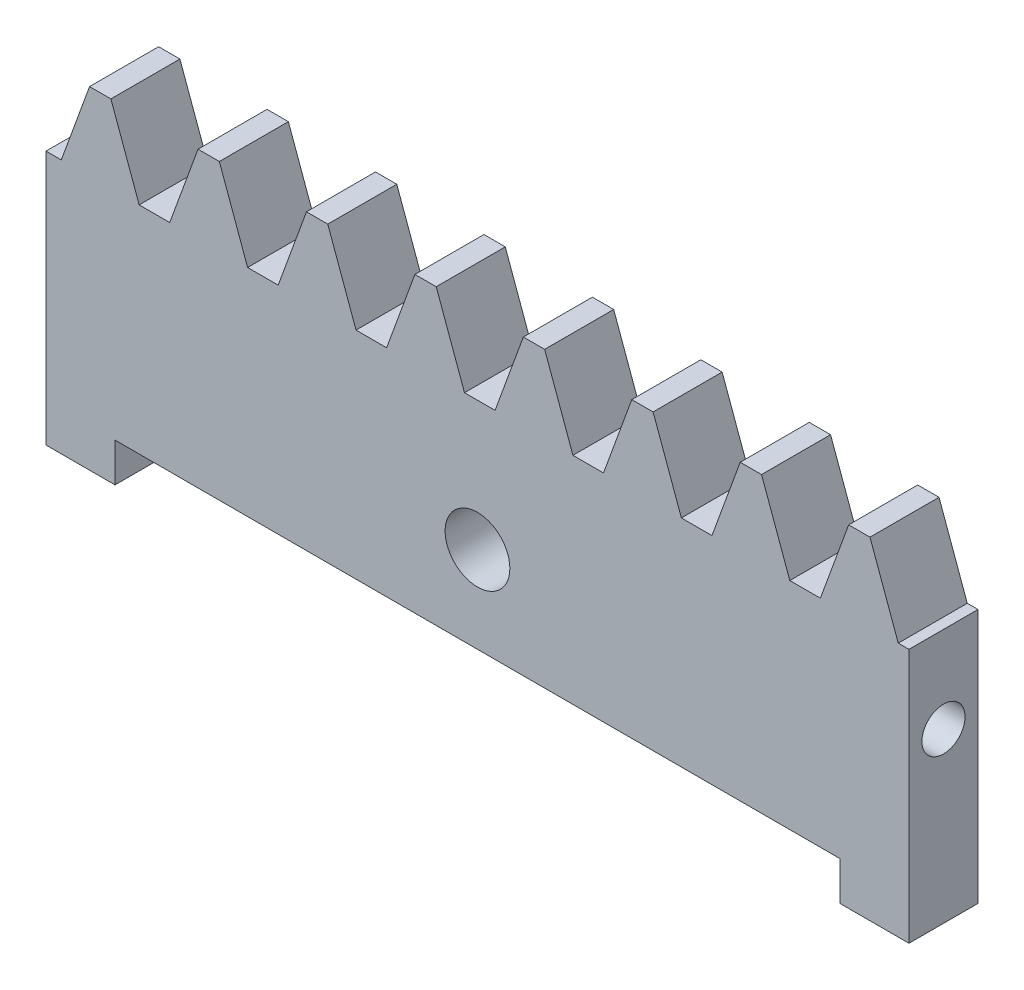
SolidWorks part; units mm, degrees
extrude "Blank" add sketch "BlankSke" against normal blind 10.16
sketch "BlankSke" plane through (0, 0, 0) normal (0, 0, 1) x (1, 0, 0)
  line L1 (0, 0) -> (127, 0)
  line L2 (0, 0) -> (0, 43.18)
  line L3 (0, 43.18) -> (127, 43.18)
  line L4 (127, 0) -> (127, 43.18)
  dimension "Length" = 127
  dimension "Blank_height" = 43.18
ref_plane "Plane1" through (0, 0, 0) normal (0, 0, 1) x (1, 0, 0)
ref_plane "Plane2" through (0, 0, 0) normal (0, 1, 0) x (1, 0, 0)
ref_plane "Plane3" through (0, 0, 0) normal (1, 0, 0) x (0, 0, -1)
other "Configuration Table"
sketch "HoldingSke" plane through (0, 0, 0) normal (0, 1, 0) x (1, 0, 0)
  line L0 (0, 0) -> (97.2876, -81.634)
  line L1 (-15, 0) -> (100, 0) construction
  line L2 (0, 0) -> (-2.1039, 2.3779)
  line L3 (0, 0) -> (-11.863, 4.5341)
  line L4 (0, 0) -> (8.5297, 1.351)
  line L5 (0, 0) -> (-23.7986, -8.8762)
  line L6 (0, 0) -> (-10.5278, -7.1032)
  line L9 (-71.009, 38.7566) -> (48.332, 82.1932)
  line L10 (-76.2, 71.12) -> (-38.1, 71.12)
  line L11 (0, 0) -> (-10.16, 0)
  line L12 (-76.2, 101.6) -> (-76.0095, 101.6)
  line L13 (24.9733, 27.94) -> (52.9518, 28.4284)
  line L14 (24.9733, 27.94) -> (24.9746, 27.94)
  line L15 (24.9733, 27.94) -> (100.4006, 29.5858)
  circle A0 centre (0, 0) radius 19.05
  circle A1 centre (0, 0) radius 19.05
  circle A2 centre (0, 0) radius 12.7
  dimension "MPH" = 38.1
  dimension "Diameter" = 38.1
  dimension "Num_teeth" = 9
  dimension "Pitch" = 127
  dimension "Show_teeth" = 400
  dimension "Thickness" = 12.7
  dimension "Ap" = 20
  dimension "Pitch_height" = 38.1
  dimension "Width" = 10.16
  dimension "Backlash" = 0.1905
  dimension "Addendum_fac" = 1
  dimension "Dedendum_fac" = 1.25
  dimension "Clearance_fac" = 0.25
  dimension "Dedendum_add" = 0.0013
  dimension "Length" = 127
sketch "TooCutSkeIll" plane through (0, 0, 0) normal (0, 0, 1) x (1, 0, 0)
  line L0 (-6.3616, 43.0463) -> (-2.5546, 32.5865)
  line L1 (-1.36, 31.75) -> (1.36, 31.75)
  line L2 (2.5546, 32.5865) -> (6.3616, 43.0463)
  line L3 (127, 43.18) -> (0, 43.18) construction
  line L4 (0, 0) -> (0, 64.897) construction
  line L5 (-13.208, 38.1) -> (12.954, 38.1) construction
  line L6 (0, 0) -> (127, 0) construction
  line L7 (4.5613, 38.1) -> (4.5613, 48.7463) construction
  line L8 (-4.5613, 38.1) -> (-4.5613, 48.7463) construction
  line L9 (6.5526, 43.18) -> (6.5526, 43.2054)
  line L10 (-6.5526, 43.18) -> (-6.5526, 43.2054)
  line L11 (-6.5526, 43.2054) -> (6.5526, 43.2054)
  arc A0 (1.36, 31.75) -> (2.5546, 32.5865) centre (1.36, 33.0213) ccw
  arc A1 (-2.5546, 32.5865) -> (-1.36, 31.75) centre (-1.36, 33.0213) ccw
  arc A2 (6.5526, 43.18) -> (6.3616, 43.0463) centre (6.5526, 42.9768) ccw
  arc A3 (-6.3616, 43.0463) -> (-6.5526, 43.18) centre (-6.5526, 42.9768) ccw
  dimension "Pitch_height" = 38.1
  dimension "Addendum_plus" = 5.1054
  dimension "Pressure_angle" = 20
  dimension "Gap_width" = 9.1226
  dimension "Dedendum" = 6.35
extrude "ToothCutIll" [suppressed] cut sketch "TooCutSkeIll" against normal through all
sketch "TooCutSkeSim" plane through (0, 0, 0) normal (0, 0, 1) x (1, 0, 0)
  line L0 (2.2501, 31.75) -> (-2.2501, 31.75)
  line L1 (6.4195, 43.2054) -> (2.2501, 31.75)
  line L2 (0, 17.4625) -> (0, 53.467) construction
  line L3 (6.4195, 43.2054) -> (-6.4195, 43.2054)
  line L6 (-6.4195, 43.2054) -> (-2.2501, 31.75)
  line L9 (-4.5613, 38.1) -> (4.5613, 38.1) construction
  line L10 (0, 0) -> (127, 0) construction
  line L11 (4.5613, 38.1) -> (4.5613, 53.467) construction
  line L12 (-4.5613, 38.1) -> (-4.5613, 53.467) construction
  dimension "Pitch_height" = 38.1
  dimension "Addendum_plus" = 5.1054
  dimension "Pressure_angle" = 20
  dimension "Gap_width" = 9.1226
  dimension "Dedendum" = 6.35
extrude "ToothCutSim" cut sketch "TooCutSkeSim" against normal through all
pattern_linear "TeethCuts" count 9 spacing 15.9593 along (1, 0, 0) of "ToothCutIll", "ToothCutSim"
sketch "Sketch1" plane through (0, 0, 0) normal (0, -1, 0) x (1, 0, 0)
  line L0 (0, -10.16) -> (127, -10.16) construction
  line L1 (0, 0) -> (10.16, 0)
  line L2 (0, 0) -> (0, -10.16)
  line L3 (0, -10.16) -> (10.16, -10.16)
  line L4 (10.16, 0) -> (10.16, -10.16)
  line L6 (127, 0) -> (116.84, 0)
  line L7 (127, 0) -> (127, -10.16)
  line L8 (127, -10.16) -> (116.84, -10.16)
  line L9 (116.84, 0) -> (116.84, -10.16)
  dimension "D1" = 10.16
sketch "Sketch4" plane through (0, 0, 0) normal (-1, 0, 0) x (0, 0, 1)
  line L0 (-10.16, 0) -> (0, 0) construction
  line L1 (-10.16, 31.75) -> (-10.16, 0) construction
  circle A0 centre (-5.08, 19.05) radius 3.175
  dimension "D2" = 6.35
  dimension "D1" = 19.05
  dimension "D3" = 5.08
extrude "Cut-Extrude2" cut sketch "Sketch4" against normal through all
extrude "Boss-Extrude1" add sketch "Sketch1" along normal blind 5.715
sketch "Sketch5" plane through (0, 0, 0) normal (0, 0, 1) x (1, 0, 0)
  line L0 (10.16, 0) -> (116.84, 0) construction
  circle A0 centre (63.5, 12.7) radius 4.7625
  dimension "D1" = 9.525
  dimension "D2" = 12.7
extrude "Cut-Extrude3" cut sketch "Sketch5" against normal through all
equation "' \"Pitch@HoldingSke\" = 4"
equation "' \"Num_teeth@HoldingSke\" = 12"
equation "' \"Ap@HoldingSke\" =  20"
equation "' \"Ap@HoldingSke\" = 20"
equation "' \"Width@HoldingSke\" = 0.25"
equation "' \"Show_teeth@HoldingSke\" = 500"
equation "' \"Backlash@HoldingSke\" = 0.009"
equation "' \"Addendum_fac@HoldingSke\" = 1.0"
equation "' \"Dedendum_fac@HoldingSke\" = 1.25"
equation "' \"Dedendum_add@HoldingSke\" = 0.00005"
equation "' \"Clearance_fac@HoldingSke\" = 0.25"
equation "' \"Pitch_height@HoldingSke\" = 1"
equation "' \"Length@HoldingSke\" = 4.71"
equation "\"MPH@HoldingSke\" = \"Dedendum_fac@HoldingSke\" / \"Pitch@HoldingSke\" + 2 * \"Dedendum_add@HoldingSke\" + 0.002"
equation "\"MPH@HoldingSke\" = ((sgn( \"MPH@HoldingSke\" - \"Pitch_height@HoldingSke\")+1)*( \"MPH@HoldingSke\" - \"Pitch_height@HoldingSke\"))/2 + \"Pitch_height@HoldingSke\""
equation "\"Blank_height@BlankSke\" = \"Pitch_height@HoldingSke\" + \"Addendum_fac@HoldingSke\"  / \"Pitch@HoldingSke\" "
equation "\"Length@BlankSke\" =  \"Length@HoldingSke\""
equation "\"Face_width@Blank\" = \"Width@HoldingSke\""
equation "\"Pressure_angle@TooCutSkeIll\" = \"Ap@HoldingSke\""
equation "\"Addendum_plus@TooCutSkeIll\" =  \"Addendum_fac@HoldingSke\"  / \"Pitch@HoldingSke\" + 0.001"
equation "\"Dedendum@TooCutSkeIll\" = \"Dedendum_fac@HoldingSke\"  / \"Pitch@HoldingSke\""
equation "\"Pitch_height@TooCutSkeIll\" =  \"MPH@HoldingSke\""
equation "\"Gap_width@TooCutSkeIll\" = 3.14159265 / 2 / \"Pitch@HoldingSke\" + 6 * \"Backlash@HoldingSke\""
equation "\"Pressure_angle@TooCutSkeSim\" = \"Ap@HoldingSke\""
equation "\"Addendum_plus@TooCutSkeSim\" =  \"Addendum_fac@HoldingSke\"  / \"Pitch@HoldingSke\" + 0.001"
equation "\"Dedendum@TooCutSkeSim\" = \"Dedendum_fac@HoldingSke\"  / \"Pitch@HoldingSke\""
equation "\"Pitch_height@TooCutSkeSim\" =  \"MPH@HoldingSke\""
equation "\"Gap_width@TooCutSkeSim\" = 3.14159265 / 2 / \"Pitch@HoldingSke\" + 6 * \"Backlash@HoldingSke\""
equation "\"Root_fillet@TooCutSkeIll\" = \"Clearance_fac@HoldingSke\" / \"Pitch@HoldingSke\" + \"Dedendum_add@HoldingSke\""
equation "\"Break_rad@TooCutSkeIll\" = 0.02 / \"Pitch@HoldingSke\" * 2"
equation "\"Linear_pitch@TeethCuts\" = 3.14159265 / \"Pitch@HoldingSke\""
equation "\"Num_teeth@HoldingSke\" = int( ( \"Length@HoldingSke\" + 0 ) / (3.14159265 / \"Pitch@HoldingSke\")) + 0.9999  + 1"
equation " \"Num_teeth@TeethCuts\" = int( \"Show_teeth@HoldingSke\" ) + 1"
equation " \"Num_teeth@TeethCuts\" = ((sgn( \"Num_teeth@TeethCuts\" - \"Num_teeth@HoldingSke\" )-1)*( \"Num_teeth@TeethCuts\" - \"Num_teeth@HoldingSke\" ))/-2+ \"Num_teeth@HoldingSke\""
equation " \"Num_teeth@TeethCuts\" = ((sgn( \"Num_teeth@TeethCuts\" - 2.0)+1)*( \"Num_teeth@TeethCuts\" - 2.0))/2 +2.0"
